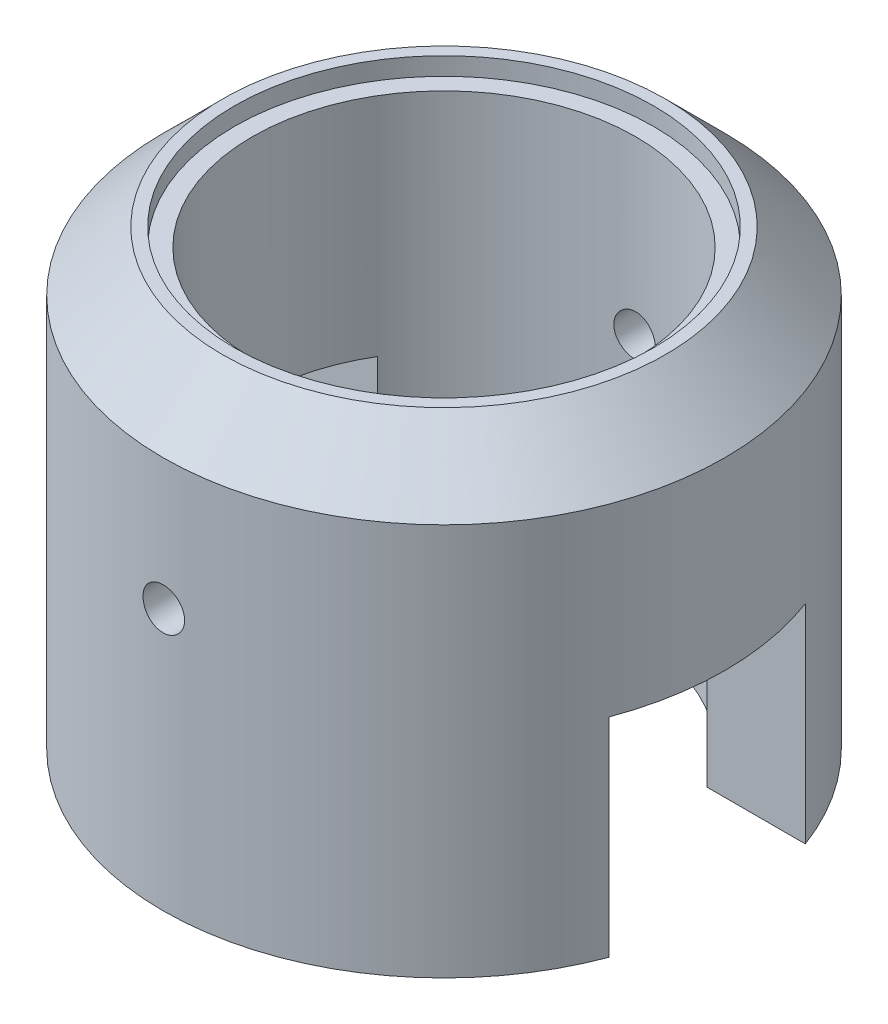
SolidWorks part; units mm, degrees
ref_plane "Front Plane" through (0, 0, 0) normal (0, 0, 1) x (1, 0, 0)
ref_plane "Top Plane" through (0, 0, 0) normal (0, 1, 0) x (1, 0, 0)
ref_plane "Right Plane" through (0, 0, 0) normal (1, 0, 0) x (0, 0, -1)
sketch "Sketch1" plane through (0, 0, 0) normal (0, 0, 1) x (1, 0, 0)
  line L0 (0, 7.6118) -> (0, -0.7865) construction
  line L1 (-4.725, 0) -> (-4.725, 7.6)
  line L2 (-4.725, 7.6) -> (-3.525, 7.6)
  line L3 (-3.525, 7.6) -> (-3.525, 7.3)
  line L4 (-3.525, 7.3) -> (-3.225, 7.3)
  line L5 (-3.225, 7.3) -> (-3.225, 0)
  line L6 (-3.225, 0) -> (-4.725, 0)
  dimension "D1" = 7.05
  dimension "D2" = 0.3
  dimension "D3" = 1.5
  dimension "D4" = 0.3
  dimension "D5" = 7.6
revolve "Revolve1" add sketch "Sketch1" angle 360 about L0
chamfer "Chamfer1" distance 1 angle 45 1 edges at (0, 7.6, 4.725)
sketch "Sketch2" plane through (0, 0, 0) normal (1, 0, 0) x (0, 0, -1)
  line L0 (-4.725, 0) -> (4.725, 0) construction
  line L1 (-1.65, 0) -> (1.65, 0)
  line L2 (-1.65, 0) -> (-1.65, 3.5)
  line L3 (-1.65, 3.5) -> (1.65, 3.5)
  line L4 (1.65, 0) -> (1.65, 3.5)
  line L5 (0, 0) -> (0, 3.916) construction
  dimension "D1" = 3.5
  dimension "D2" = 3.3
extrude "Cut-Extrude1" cut sketch "Sketch2" against normal through all and the other way through all
sketch "Sketch3" plane through (0, 0, 0) normal (0, 0, 1) x (1, 0, 0)
  circle A0 centre (0, 4.4) radius 0.35
  point P2 (0, 0)
  point P4 (1.1791, 3.2954)
  dimension "D1" = 0.7
  dimension "D2" = 4.4
extrude "Cut-Extrude2" cut sketch "Sketch3" against normal through all and the other way through all
